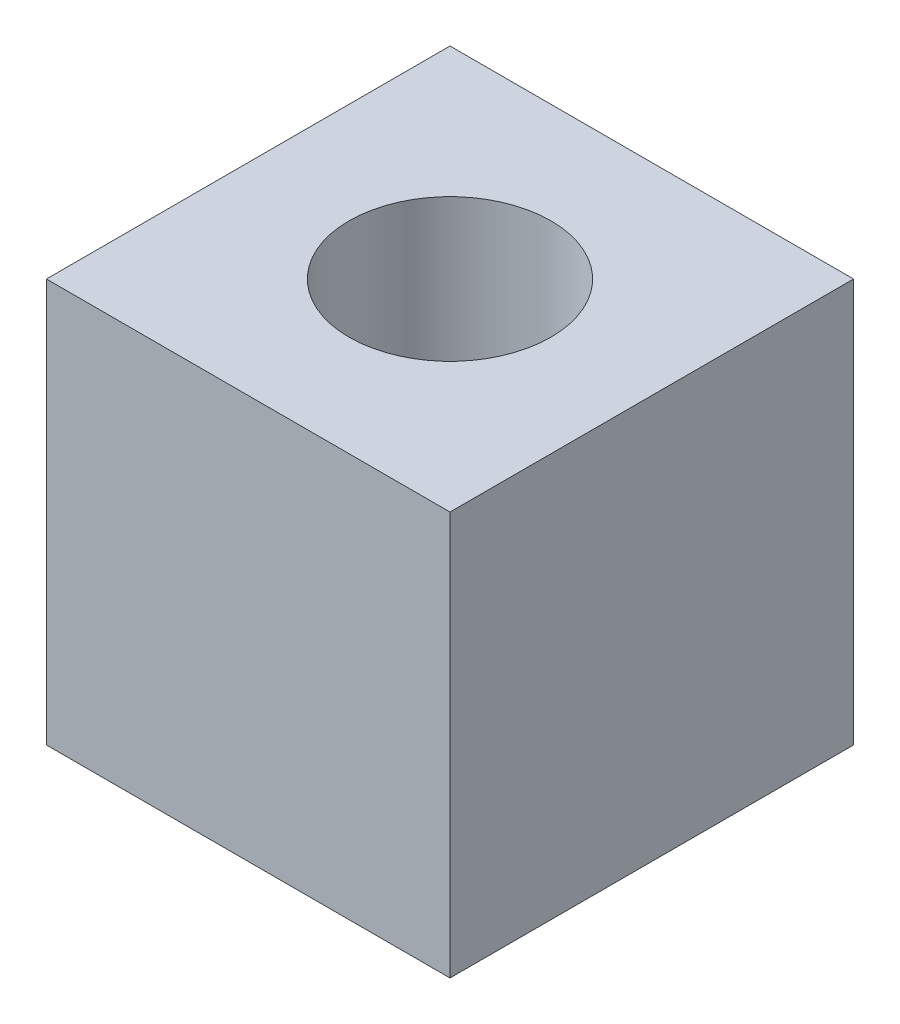
SolidWorks part; units mm, degrees
ref_plane "Front Plane" through (0, 0, 0) normal (0, 0, 1) x (1, 0, 0)
ref_plane "Top Plane" through (0, 0, 0) normal (0, 1, 0) x (1, 0, 0)
ref_plane "Right Plane" through (0, 0, 0) normal (1, 0, 0) x (0, 0, -1)
sketch "Sketch1" plane through (0, 0, 0) normal (0, 0, 1) x (1, 0, 0)
  line L1 (0, 0) -> (50.8, 0)
  line L2 (0, 0) -> (0, -50.8)
  line L3 (0, -50.8) -> (50.8, -50.8)
  line L4 (50.8, 0) -> (50.8, -50.8)
  dimension "D1" = 50.8
  dimension "D2" = 50.8
extrude "Boss-Extrude1" add sketch "Sketch1" along normal blind 50.8
sketch "Sketch2" plane through (0, 0, 0) normal (0, 1, 0) x (1, 0, 0)
  line L0 (25.4, 6.2071) -> (25.4, -55.3635) construction
  line L1 (-8.7357, -25.4) -> (60.2943, -25.4) construction
  line L2 (0, -50.8) -> (0, 0) construction
  line L3 (50.8, 0) -> (0, 0) construction
  circle A0 centre (25.4, -25.4) radius 12.7
  dimension "D1" = 25.4
  dimension "D2" = 25.4
  dimension "D3" = 25.4
extrude "Cut-Extrude1" cut sketch "Sketch2" against normal up to next
